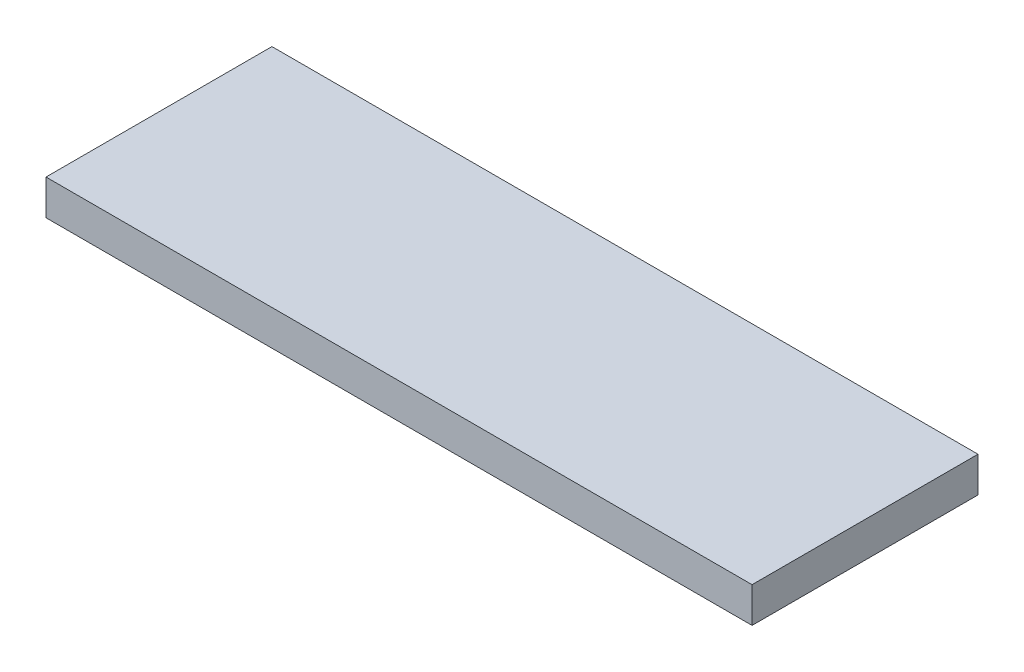
SolidWorks part; units mm, degrees
ref_plane "Alzado" through (0, 0, 0) normal (0, 0, 1) x (1, 0, 0)
ref_plane "Planta" through (0, 0, 0) normal (0, 1, 0) x (1, 0, 0)
ref_plane "Vista lateral" through (0, 0, 0) normal (1, 0, 0) x (0, 0, -1)
sketch "Croquis1" plane through (0, 0, 0) normal (0, 1, 0) x (1, 0, 0)
  line L1 (-50, -16) -> (50, -16)
  line L2 (-50, -16) -> (-50, 16)
  line L3 (-50, 16) -> (50, 16)
  line L4 (50, -16) -> (50, 16)
  line L5 (-50, -16) -> (50, 16) construction
  line L6 (-50, 16) -> (50, -16) construction
  point P0 (0, 0)
  dimension "D1" = 100
  dimension "D2" = 32
extrude "Saliente-Extruir1" add sketch "Croquis1" along normal blind 5
